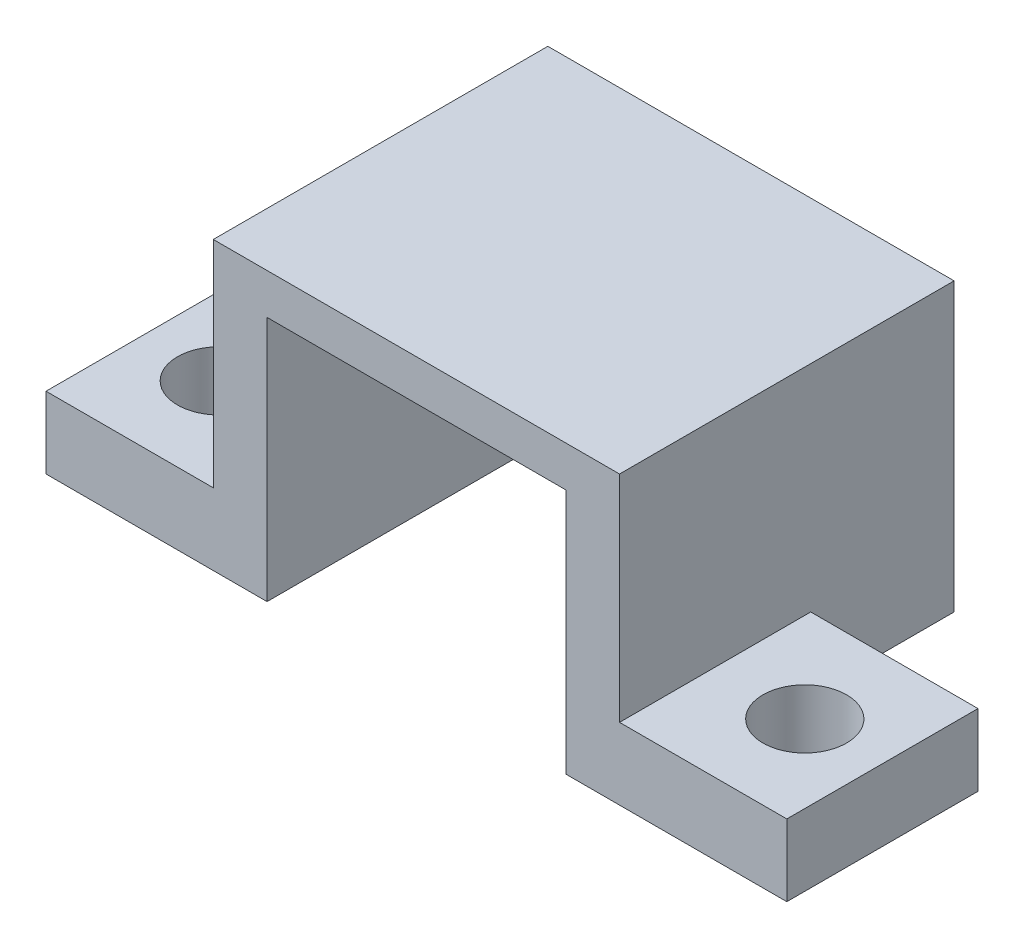
SolidWorks part; units mm, degrees
ref_plane "Plano frontal" through (0, 0, 0) normal (0, 0, 1) x (1, 0, 0)
ref_plane "Plano superior" through (0, 0, 0) normal (0, 1, 0) x (1, 0, 0)
ref_plane "Plano direito" through (0, 0, 0) normal (1, 0, 0) x (0, 0, -1)
ref_plane "Plano1" through (0, 0.0001, 0) normal (0, -1, 0) x (1, 0, 0)
sketch "Esboço1" plane through (0, 0.0001, 0) normal (0, -1, 0) x (1, 0, 0)
  line L0 (24, 0) -> (24, 14)
  line L1 (24, 14) -> (7, 14)
  line L2 (7, 14) -> (7, 0)
  line L3 (7, 0) -> (24, 0)
extrude "Ressalto-extrusão1" add sketch "Esboço1" against normal blind 12
sketch "Esboço2" plane through (0, 0, 14) normal (0, 0, 1) x (1, 0, 0)
  line L0 (9.25, 0.0001) -> (21.75, 0.0001)
  line L1 (21.75, 0.0001) -> (21.75, 10.3001)
  line L2 (21.75, 10.3001) -> (9.25, 10.3001)
  line L3 (9.25, 10.3001) -> (9.25, 0.0001)
extrude "Corte-extrusão1" cut sketch "Esboço2" against normal through all
sketch "Esboço3" plane through (7, 0, 0) normal (-1, 0, 0) x (0, 0, 1)
  line L0 (14, 3.0001) -> (14, 0.0001)
  line L1 (14, 0.0001) -> (6, 0.0001)
  line L2 (6, 0.0001) -> (6, 3.0001)
  line L3 (6, 3.0001) -> (14, 3.0001)
extrude "Ressalto-extrusão2" add sketch "Esboço3" along normal blind 7
sketch "Esboço4" plane through (0, 0.0001, 0) normal (0, -1, 0) x (1, 0, 0)
  line L38 (3.25, 11.75) -> (3.25, 8.25) construction
  line L44 (1.0729, 10) -> (5.4272, 10) construction
  circle A0 centre (3.25, 10) radius 1.75
  point P1 (3.25, 10)
  dimension "D1" = 3.5
extrude "Corte-extrusão2" cut sketch "Esboço4" against normal through all
sketch "Esboço5" plane through (24, 0, 0) normal (1, 0, 0) x (0, 0, -1)
  line L0 (-6, 3.0001) -> (-6, 0.0001)
  line L1 (-6, 0.0001) -> (-14, 0.0001)
  line L2 (-14, 0.0001) -> (-14, 3.0001)
  line L3 (-14, 3.0001) -> (-6, 3.0001)
extrude "Ressalto-extrusão3" add sketch "Esboço5" along normal blind 7
sketch "Esboço6" plane through (0, 0.0001, 0) normal (0, -1, 0) x (1, 0, 0)
  line L38 (25.5043, 10) -> (29.8773, 10) construction
  line L40 (27.7514, 11.9181) -> (27.7514, 8.3486) construction
  circle A0 centre (27.7514, 10) radius 1.75
  dimension "D1" = 3.5
extrude "Corte-extrusão3" cut sketch "Esboço6" against normal through all
